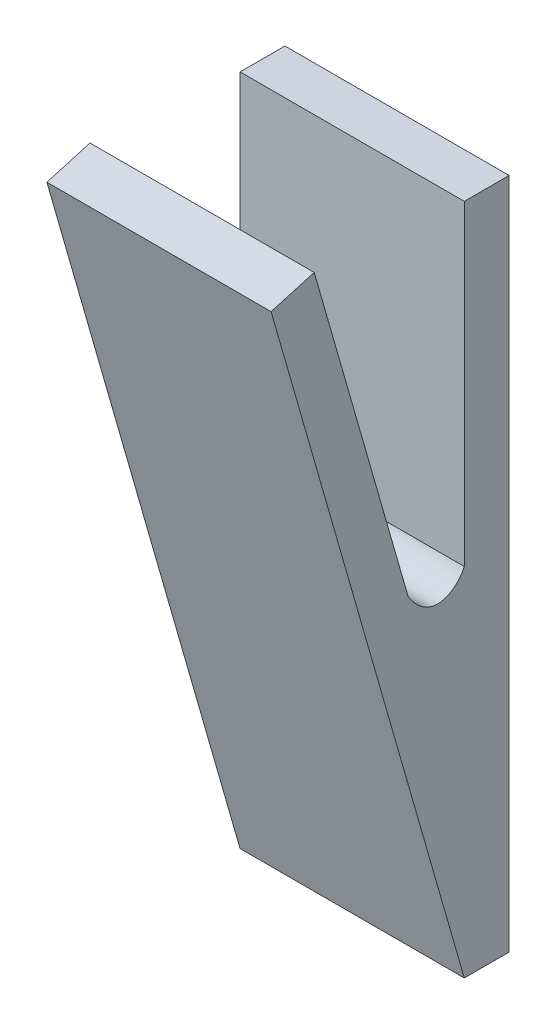
SolidWorks part; units mm, degrees
material "Maple"
ref_plane "Wasteboard" through (0, 0, 0) normal (0, 0, 1) x (1, 0, 0)
ref_plane "Left-Right" through (0, 0, 0) normal (0, 1, 0) x (1, 0, 0)
ref_plane "Front-Back" through (0, 0, 0) normal (1, 0, 0) x (0, 0, -1)
sketch "Sketch1" plane through (0, 0, 0) normal (0, 0, 1) x (1, 0, 0)
  line L1 (-5.545, 20.3555) -> (4.455, 20.3555)
  line L2 (-5.545, 20.3555) -> (-5.545, -9.6445)
  line L3 (-5.545, -9.6445) -> (4.455, -9.6445)
  line L4 (4.455, 20.3555) -> (4.455, -9.6445)
  dimension "D1" = 10
  dimension "D2" = 30
extrude "Boss-Extrude1" add sketch "Sketch1" along normal blind 2
ref_plane "Plane1" through (0, -1.2627, 4.4035) normal (0, -0.2756, 0.9613) x (1, 0, 0)
sketch "Sketch2" plane through (0, -1.2627, 4.4035) normal (0, -0.2756, 0.9613) x (1, 0, 0)
  line L1 (-5.545, 22.5393) -> (4.455, 22.5393)
  line L2 (-5.545, 22.5393) -> (-5.545, -8.7197)
  line L3 (-5.545, -8.7197) -> (4.455, -8.7197)
  line L4 (4.455, 22.5393) -> (4.455, -8.7197)
  dimension "D1" = 31.259
  dimension "D2" = 10
extrude "Boss-Extrude2" add sketch "Sketch2" against normal blind 2
sketch "Sketch3" plane through (-5.545, 0, 0) normal (-1, 0, 0) x (0, 0, 1)
  line L0 (2, 20.3555) -> (2, -2.3886) construction
  line L1 (8.6936, 20.9548) -> (2, -2.3886) construction
  line L2 (2, 6.2507) -> (2, -2.3886)
  line L3 (2, -2.3886) -> (4.4968, 6.3188)
  spline S0 degree 3 poles (2, 6.2507) (2.2108, 5.6819) (3.3905, 4.6185) (4.4968, 6.3188) knots 0 0 0 0 1 1 1 1
extrude "Boss-Extrude3" add sketch "Sketch3" against normal blind 10
